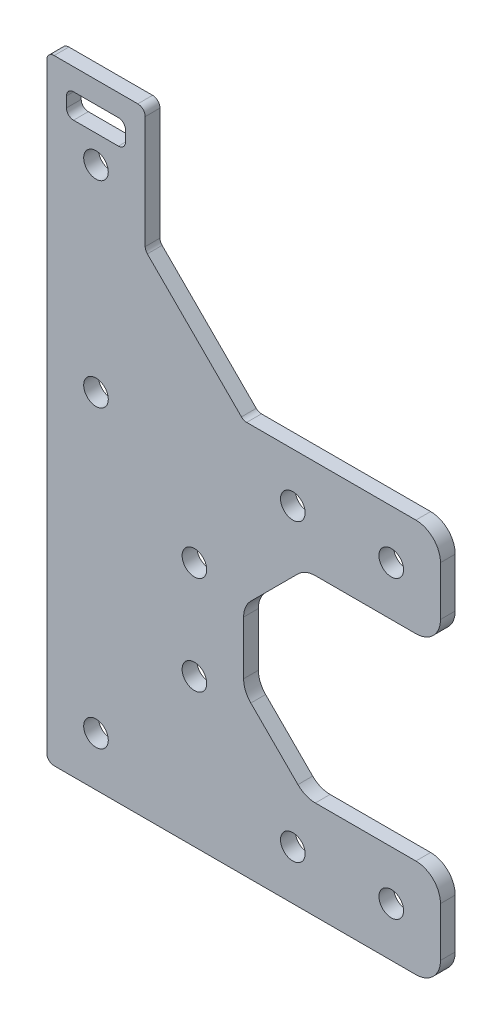
SolidWorks part; units mm, degrees
ref_plane "Front" through (0, 0, 0) normal (0, 0, 1) x (1, 0, 0)
ref_plane "Top" through (0, 0, 0) normal (0, 1, 0) x (1, 0, 0)
ref_plane "Right" through (0, 0, 0) normal (1, 0, 0) x (0, 0, -1)
sketch "Model" plane through (0, 0, 0) normal (0, 0, 1) x (1, 0, 0)
  line L0 (-36.75, 0) -> (36.75, 0)
  line L1 (-38.25, 123.5) -> (-38.25, 1.5)
  line L2 (36.75, 20) -> (16.3211, 20)
  line L3 (-34.25, 119.15) -> (-34.25, 117.03)
  line L4 (-22.25, 117.03) -> (-22.25, 119.15)
  line L5 (-18.25, 123.5) -> (-18.25, 100.6213)
  line L6 (3.2145, 31.0355) -> (12.7855, 21.4645)
  line L7 (1.75, 45.4289) -> (1.75, 34.5711)
  line L8 (36.75, 60) -> (16.3211, 60)
  line L9 (12.7855, 58.5355) -> (3.2145, 48.9645)
  line L10 (-17.8107, 99.5607) -> (1.3107, 80.4393)
  line L11 (36.75, 80) -> (2.3713, 80)
  line L12 (41.75, 5) -> (41.75, 15)
  line L13 (41.75, 65) -> (41.75, 75)
  line L14 (-32.81, 115.59) -> (-23.69, 115.59)
  line L15 (-23.69, 120.59) -> (-32.81, 120.59)
  line L16 (-19.75, 125) -> (-36.75, 125)
  line L17 (-28.25, 125) -> (-28.25, 0) construction
  line L18 (41.75, 70) -> (-38.25, 70) construction
  line L19 (41.75, 10) -> (-38.25, 10) construction
  line L20 (1.75, 40) -> (-38.25, 40) construction
  arc A0 (12.7855, 21.4645) -> (16.3211, 20) centre (16.3211, 25) ccw
  arc A1 (1.75, 34.5711) -> (3.2145, 31.0355) centre (6.75, 34.5711) ccw
  arc A2 (3.2145, 48.9645) -> (1.75, 45.4289) centre (6.75, 45.4289) ccw
  arc A3 (16.3211, 60) -> (12.7855, 58.5355) centre (16.3211, 55) ccw
  arc A4 (36.75, 0) -> (41.75, 5) centre (36.75, 5) ccw
  arc A5 (41.75, 15) -> (36.75, 20) centre (36.75, 15) ccw
  arc A6 (41.75, 75) -> (36.75, 80) centre (36.75, 75) ccw
  arc A7 (36.75, 60) -> (41.75, 65) centre (36.75, 65) ccw
  circle A8 centre (-28.25, 70) radius 2.5
  circle A9 centre (-8.25, 30) radius 2.5
  circle A10 centre (-8.25, 50) radius 2.5
  circle A11 centre (11.75, 70) radius 2.5
  circle A12 centre (31.75, 70) radius 2.5
  circle A13 centre (31.75, 10) radius 2.5
  circle A14 centre (11.75, 10) radius 2.5
  circle A15 centre (-28.25, 10) radius 2.5
  circle A16 centre (-28.25, 110) radius 2.5
  arc A17 (-18.25, 100.6213) -> (-17.8107, 99.5607) centre (-16.75, 100.6213) ccw
  arc A18 (1.3107, 80.4393) -> (2.3713, 80) centre (2.3713, 81.5) ccw
  arc A19 (-18.25, 123.5) -> (-19.75, 125) centre (-19.75, 123.5) ccw
  arc A20 (-36.75, 125) -> (-38.25, 123.5) centre (-36.75, 123.5) ccw
  arc A21 (-38.25, 1.5) -> (-36.75, 0) centre (-36.75, 1.5) ccw
  arc A22 (-32.81, 120.59) -> (-34.25, 119.15) centre (-32.81, 119.15) ccw
  arc A23 (-22.25, 119.15) -> (-23.69, 120.59) centre (-23.69, 119.15) ccw
  arc A24 (-23.69, 115.59) -> (-22.25, 117.03) centre (-23.69, 117.03) ccw
  arc A25 (-34.25, 117.03) -> (-32.81, 115.59) centre (-32.81, 117.03) ccw
  point P74 (-28.25, 115.59)
  point P79 (0, 0)
  dimension "D1" = 5
  dimension "D2" = 1.5
  dimension "D3" = 125
  dimension "D6" = 5
  dimension "D7" = 20
  dimension "D15" = 1.44
  dimension "D24" = 40
  dimension "D4" = 20
  dimension "D5" = 80
  dimension "D8" = 20
  dimension "D9" = 40
  dimension "D10" = 135
  dimension "D11" = 27.0416
  dimension "D12" = 15
  dimension "D13" = 10
  dimension "D14" = 30
  dimension "D16" = 5
  dimension "D17" = 12
  dimension "D18" = 4.41
  dimension "D19" = 30
  dimension "D20" = 20
  dimension "D21" = 10.8579
  dimension "D22" = 13.5355
  dimension "D23" = 135
  dimension "D25" = 10
extrude "Boss-Extrude1" add sketch "Model" along normal blind 3
